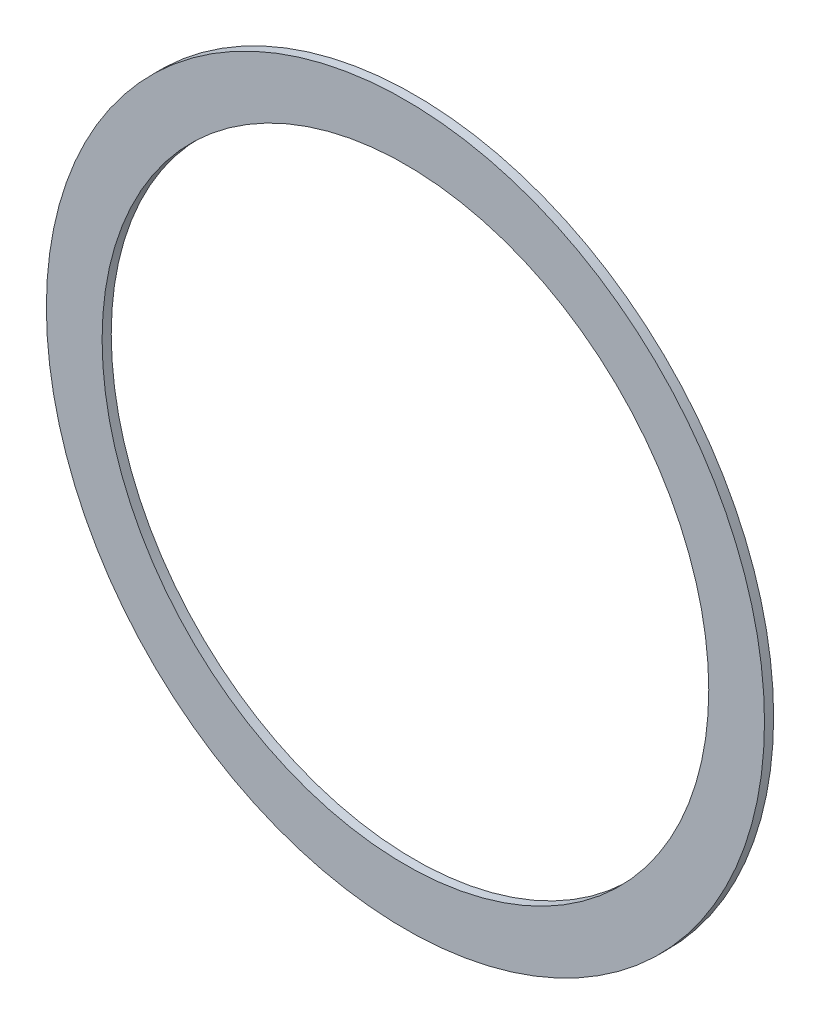
SolidWorks part; units mm, degrees
ref_plane "Plan de face" through (0, 0, 0) normal (0, 0, 1) x (1, 0, 0)
ref_plane "Plan de dessus" through (0, 0, 0) normal (0, 1, 0) x (1, 0, 0)
ref_plane "Plan de droite" through (0, 0, 0) normal (1, 0, 0) x (0, 0, -1)
sketch "Esquisse1" plane through (0, 0, 0) normal (0, 0, 1) x (1, 0, 0)
  circle A0 centre (0, 0) radius 33 construction
  circle A1 centre (0, 0) radius 39.5 construction
  circle A2 centre (0, 0) radius 39.3
  circle A3 centre (0, 0) radius 33.2
  dimension "D2" = 66
  dimension "D3" = 79
  dimension "D1" = 0.2
  dimension "D4" = 0.2
extrude "Boss.-Extru.1" add sketch "Esquisse1" along normal blind 1
equation "\"D1@Esquisse1\"=\"D4@Esquisse1\""
